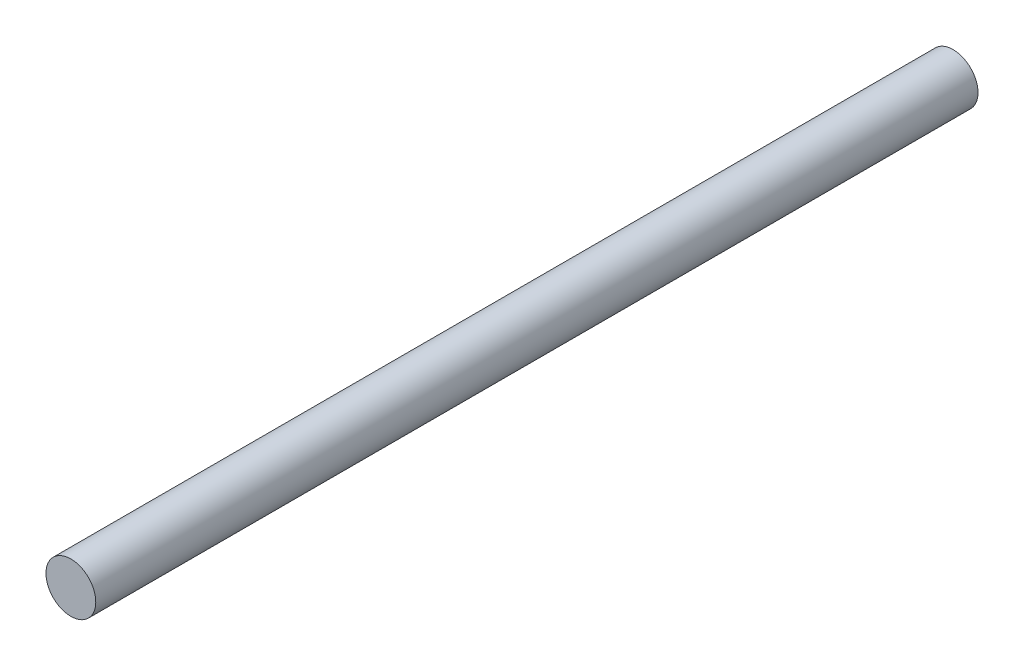
SolidWorks part; units mm, degrees
ref_plane "Alzado" through (0, 0, 0) normal (0, 0, 1) x (1, 0, 0)
ref_plane "Planta" through (0, 0, 0) normal (0, 1, 0) x (1, 0, 0)
ref_plane "Vista lateral" through (0, 0, 0) normal (1, 0, 0) x (0, 0, -1)
sketch "Croquis1" plane through (0, 0, 0) normal (0, 0, 1) x (1, 0, 0)
  circle A0 centre (0, 0) radius 1.85
  dimension "D1" = 3.7
extrude "Saliente-Extruir1" add sketch "Croquis1" along normal blind 65.535
